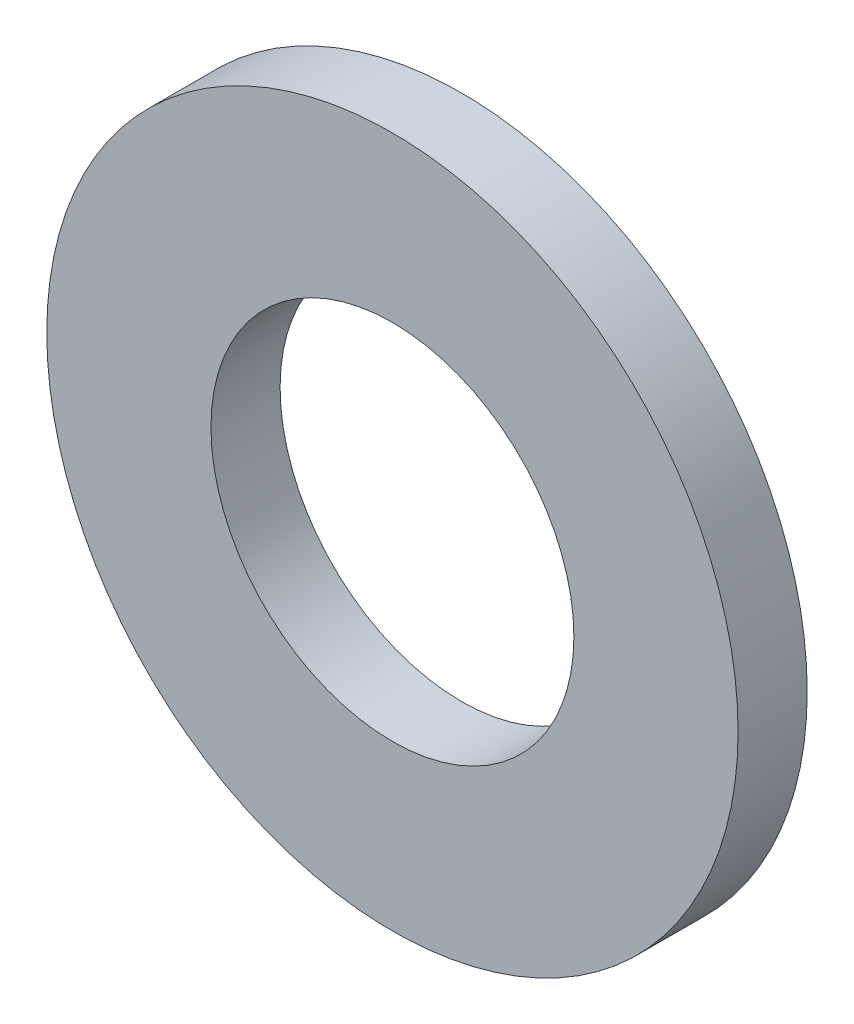
SolidWorks part; units mm, degrees
material "AISI 304"
ref_plane "Front Plane" through (0, 0, 0) normal (0, 0, 1) x (1, 0, 0)
ref_plane "Top Plane" through (0, 0, 0) normal (0, 1, 0) x (1, 0, 0)
ref_plane "Right Plane" through (0, 0, 0) normal (1, 0, 0) x (0, 0, -1)
sketch "Sketch1" plane through (0, 0, 0) normal (0, 0, 1) x (1, 0, 0)
  line L0 (0, 0) -> (0, -5.25) construction
  line L1 (0, 0) -> (3.7123, -3.7123) construction
  circle A0 centre (0, 0) radius 10
  circle A1 centre (0, 0) radius 5.25
  point P5 (10, 0)
  point P6 (5.25, 0)
  point P7 (-5.25, 0)
  point P8 (-10, 0)
  point P9 (0, 10)
  point P10 (0, 5.25)
  point P11 (0, -10)
  point P12 (0, -5.25)
  point P13 (3.7123, -3.7123)
  dimension "D1" = 45
  dimension "OD" = 20
  dimension "ID1" = 10.5
sketch "Sketch2" plane through (0, 0, 0) normal (1, 0, 0) x (0, 0, -1)
  line L0 (-1, 10) -> (1, 10) construction
  point P2 (0, 10)
  dimension "Thickness" = 2
sketch "Sketch3" plane through (0, 0, 0) normal (0, 0, 1) x (1, 0, 0)
  circle A0 centre (0, 0) radius 10 construction
  circle A1 centre (0, 0) radius 5.25 construction
  circle A2 centre (0, 0) radius 10
  circle A3 centre (0, 0) radius 5.25
extrude "Boss-Extrude1" add sketch "Sketch3" along normal up to vertex (1 mm away) and the other way up to vertex (1 mm away) up to point (0, 10, 1) other way up to point (0, 10, -1)
